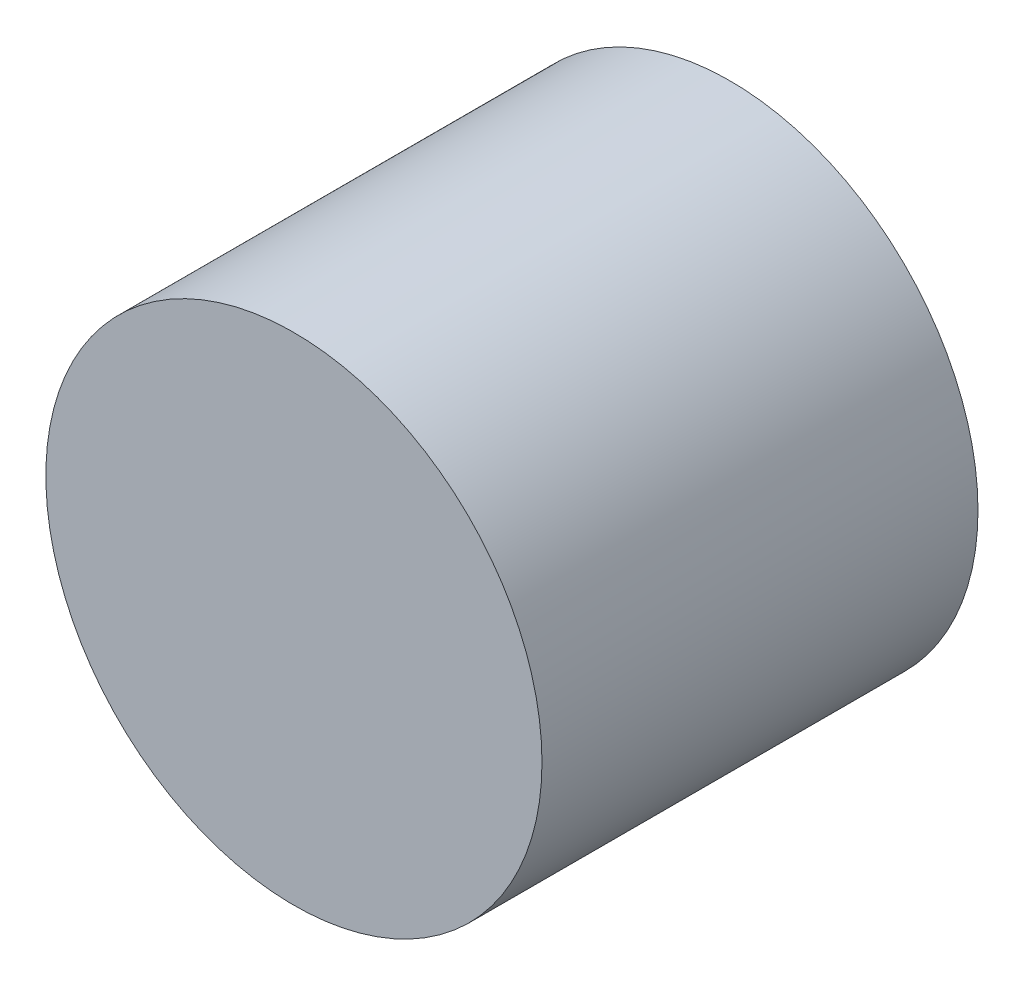
SolidWorks part; units mm, degrees
material "Plain Carbon Steel"
ref_plane "Front Plane" through (0, 0, 0) normal (0, 0, 1) x (1, 0, 0)
ref_plane "Top Plane" through (0, 0, 0) normal (0, 1, 0) x (1, 0, 0)
ref_plane "Right Plane" through (0, 0, 0) normal (1, 0, 0) x (0, 0, -1)
sketch "Sketch1" plane through (0, 0, 0) normal (0, 0, 1) x (1, 0, 0)
  circle A0 centre (0, 0) radius 16.5
  dimension "D1" = 33
extrude "Boss-Extrude2" add sketch "Sketch1" along normal mid plane 29 contours A0
